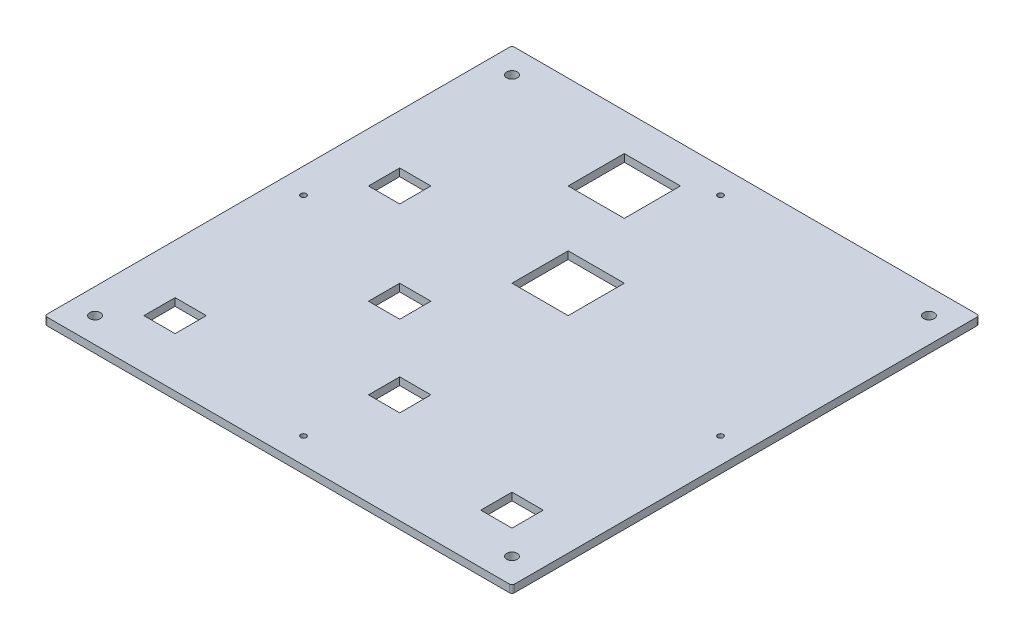
SolidWorks part; units mm, degrees
ref_plane "Plan de face" through (0, 0, 0) normal (0, 0, 1) x (1, 0, 0)
ref_plane "Plan de dessus" through (0, 0, 0) normal (0, 1, 0) x (1, 0, 0)
ref_plane "Plan de droite" through (0, 0, 0) normal (1, 0, 0) x (0, 0, -1)
sketch "Esquisse2" plane through (0, 0, 0) normal (0, 1, 0) x (1, 0, 0)
  line L1 (-92.5, 92.5) -> (92.5, 92.5)
  line L2 (-92.5, 92.5) -> (-92.5, -92.5)
  line L3 (-92.5, -92.5) -> (92.5, -92.5)
  line L4 (92.5, 92.5) -> (92.5, -92.5)
  dimension "D1" = 185
  dimension "D2" = 185
  dimension "D3" = 92.5
  dimension "D4" = 92.5
extrude "Boss.-Extru.1" add sketch "Esquisse2" against normal blind 3
sketch "Esquisse3" plane through (0, 0, 0) normal (0, 1, 0) x (1, 0, 0)
  line L0 (-77.77, 77.77) -> (77.77, 77.77)
  line L1 (-92.5, 92.5) -> (92.5, 92.5)
  line L2 (-92.5, 92.5) -> (-92.5, -92.5)
  line L3 (-92.5, -92.5) -> (92.5, -92.5)
  line L4 (92.5, 92.5) -> (92.5, -92.5)
  line L8 (77.77, 77.77) -> (77.77, -77.77)
  line L9 (-77.77, -77.77) -> (77.77, -77.77)
  line L10 (-77.77, 77.77) -> (-77.77, -77.77)
  dimension "D2" = 155.54
  dimension "D3" = 155.54
  dimension "D1" = 14.73
extrude "Boss.-Extru.2" add sketch "Esquisse3" along normal blind 40
sketch "Esquisse4" plane through (0, 0, 0) normal (0, 1, 0) x (1, 0, 0)
  line L0 (-55.55, 77.77) -> (-33.33, 77.77)
  line L1 (77.77, 77.77) -> (-77.77, 77.77) construction
  line L2 (-33.33, 77.77) -> (-33.33, 55.55)
  line L3 (-33.33, 55.55) -> (11.11, 55.55)
  line L4 (11.11, 55.55) -> (11.11, 33.33)
  line L5 (11.11, 33.33) -> (-11.11, 33.33)
  line L6 (-11.11, 33.33) -> (-11.11, -11.11)
  line L8 (-33.33, -11.11) -> (-33.33, -55.55)
  line L9 (-33.33, -55.55) -> (-55.55, -55.55)
  line L13 (-33.33, -11.11) -> (-11.11, -11.11)
  line L14 (-55.55, 77.77) -> (-55.55, 33.33)
  line L15 (-55.55, 33.33) -> (-33.33, 33.33)
  line L16 (-33.33, 33.33) -> (-33.33, 11.11)
  line L17 (-33.33, 11.11) -> (-55.55, 11.11)
  line L18 (-55.55, 11.11) -> (-55.55, -55.55)
  line L19 (-77.77, 77.77) -> (-77.77, -77.77) construction
  line L20 (-77.77, -77.77) -> (77.77, -77.77) construction
  line L21 (77.77, -77.77) -> (77.77, 77.77) construction
  line L22 (33.33, 55.55) -> (55.55, 55.55)
  line L23 (33.33, 55.55) -> (33.33, -33.33)
  line L25 (55.55, 55.55) -> (55.55, -55.55)
  line L28 (55.55, -55.55) -> (33.33, -55.55)
  line L30 (33.33, -33.33) -> (11.11, -33.33)
  line L32 (33.33, -77.77) -> (11.11, -77.77)
  line L33 (11.11, -33.33) -> (11.11, -77.77)
  line L34 (33.33, -55.55) -> (33.33, -77.77)
  line L35 (77.77, -77.77) -> (77.77, 77.77) construction
  dimension "D1" = 22.22
  dimension "D2" = 22.22
  dimension "D3" = 22.22
  dimension "D4" = 22.22
  dimension "D5" = 22.22
  dimension "D6" = 22.22
  dimension "D7" = 22.22
  dimension "D8" = 22.22
  dimension "D9" = 22.22
  dimension "D10" = 66.66
  dimension "D11" = 22.22
  dimension "D12" = 22.22
  dimension "D13" = 22.22
  dimension "D14" = 22.22
  dimension "D15" = 22.22
  dimension "D16" = 22.22
  dimension "D17" = 22.22
  dimension "D18" = 44.44
extrude "Boss.-Extru.3" add sketch "Esquisse4" along normal blind 20
sketch "Esquisse5" plane through (0, 0, 0) normal (0, 1, 0) x (1, 0, 0)
  line L0 (77.77, 77.77) -> (-33.33, 77.77) construction
  line L1 (-33.33, 55.55) -> (-11.11, 55.55)
  line L2 (-33.33, 55.55) -> (-33.33, 77.77)
  line L3 (-33.33, 77.77) -> (-11.11, 77.77)
  line L4 (-11.11, 55.55) -> (-11.11, 77.77)
  line L5 (-11.11, -11.11) -> (-11.11, 33.33) construction
  line L6 (-11.11, 33.33) -> (11.11, 33.33)
  line L7 (-11.11, 33.33) -> (-11.11, 11.11)
  line L8 (-11.11, 11.11) -> (11.11, 11.11)
  line L9 (11.11, 33.33) -> (11.11, 11.11)
  line L10 (11.11, 33.33) -> (11.11, 55.55) construction
  line L11 (-33.33, 11.11) -> (-55.55, 11.11) construction
  line L12 (33.33, -55.55) -> (55.55, -55.55) construction
  line L13 (-33.33, -11.11) -> (-20.98, -11.11)
  line L14 (-33.33, -11.11) -> (-33.33, -23.46)
  line L15 (-33.33, -23.46) -> (-20.98, -23.46)
  line L16 (-20.98, -11.11) -> (-20.98, -23.46)
  line L17 (-72.835, 28.395) -> (-60.485, 28.395)
  line L18 (-72.835, 28.395) -> (-72.835, 16.045)
  line L19 (-72.835, 16.045) -> (-60.485, 16.045)
  line L20 (-60.485, 28.395) -> (-60.485, 16.045)
  line L21 (-72.835, -60.485) -> (-60.485, -60.485)
  line L22 (-72.835, -60.485) -> (-72.835, -72.835)
  line L23 (-72.835, -72.835) -> (-60.485, -72.835)
  line L24 (-60.485, -60.485) -> (-60.485, -72.835)
  line L25 (60.485, -60.485) -> (72.835, -60.485)
  line L26 (60.485, -60.485) -> (60.485, -72.835)
  line L27 (60.485, -72.835) -> (72.835, -72.835)
  line L28 (72.835, -60.485) -> (72.835, -72.835)
  line L29 (11.11, -55.55) -> (-1.24, -55.55)
  line L30 (11.11, -55.55) -> (11.11, -43.2)
  line L31 (11.11, -43.2) -> (-1.24, -43.2)
  line L32 (-1.24, -55.55) -> (-1.24, -43.2)
  line L34 (11.11, -33.33) -> (11.11, -77.77) construction
  line L35 (-77.77, 77.77) -> (-77.77, -77.77) construction
  line L36 (-55.55, 33.33) -> (-33.33, 33.33) construction
  line L37 (-55.55, 77.77) -> (-55.55, 33.33) construction
  line L38 (-77.77, -77.77) -> (11.11, -77.77) construction
  line L39 (77.77, -77.77) -> (77.77, 77.77) construction
  dimension "D1" = 12.35
  dimension "D2" = 12.35
  dimension "D3" = 12.35
  dimension "D4" = 12.35
  dimension "D5" = 12.35
  dimension "D6" = 12.35
  dimension "D7" = 12.35
  dimension "D8" = 12.35
  dimension "D9" = 12.35
  dimension "D10" = 12.35
  dimension "D11" = 4.935
  dimension "D12" = 4.935
  dimension "D13" = 4.935
  dimension "D14" = 4.935
  dimension "D15" = 4.935
  dimension "D16" = 4.935
extrude "Enlèv. mat.-Extru.1" cut sketch "Esquisse5" against normal up to next
fillet "Congé1" radius 1 8 edges at (-92.5, 18.5, -92.5) (-92.5, 18.5, 92.5) (-92.5, 40, 0) (0, 40, 92.5) (0, 40, -92.5) (92.5, 40, 0) (92.5, 18.5, -92.5) (92.5, 18.5, 92.5)
sketch "Esquisse6" plane through (0, 40, 0) normal (0, 1, 0) x (1, 0, 0)
  line L0 (92.5, 91.5) -> (92.5, -91.5) construction
  line L1 (-91.5, 92.5) -> (91.5, 92.5) construction
  line L2 (91.5, -92.5) -> (-91.5, -92.5) construction
  line L3 (-92.5, -91.5) -> (-92.5, 91.5) construction
  circle A0 centre (-82.5, -82.5) radius 1.1
  circle A1 centre (82.5, -82.5) radius 1.1
  circle A2 centre (82.5, 82.5) radius 1.1
  circle A3 centre (-82.5, 82.5) radius 1.1
  circle A4 centre (0, 82.5) radius 1.1
  circle A5 centre (-82.5, 0) radius 1.1
  circle A6 centre (82.5, 0) radius 1.1
  circle A7 centre (0, -82.5) radius 1.1
  dimension "D1" = 2.2
  dimension "D2" = 10
  dimension "D3" = 10
  dimension "D4" = 10
  dimension "D5" = 10
  dimension "D6" = 82.5
  dimension "D7" = 82.5
extrude "Enlèv. mat.-Extru.2" cut sketch "Esquisse6" against normal through all
sketch "Esquisse7" plane through (0, 40, 0) normal (0, 1, 0) x (1, 0, 0)
  circle A0 centre (-82.5, -82.5) radius 2.1
  circle A1 centre (-82.5, 82.5) radius 2.1
  circle A2 centre (82.5, 82.5) radius 2.1
  circle A3 centre (82.5, -82.5) radius 2.1
  dimension "D1" = 4.2
extrude "Enlèv. mat.-Extru.3" cut sketch "Esquisse7" against normal through all
sketch "Esquisse8" plane through (0, 0, 92.5) normal (0, 0, 1) x (1, 0, 0)
  line L0 (-91.5, -3) -> (91.5, -3) construction
  line L1 (114.072, 93.7402) -> (-112.4133, 93.7402)
  line L2 (114.072, 93.7402) -> (114.072, 0)
  line L3 (114.072, 0) -> (-112.4133, 0)
  line L4 (-112.4133, 93.7402) -> (-112.4133, 0)
  dimension "D1" = 3
extrude "Enlèv. mat.-Extru.4" cut sketch "Esquisse8" against normal through all
